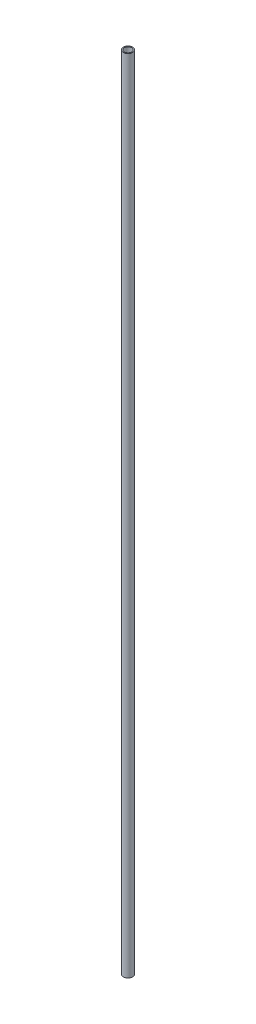
SolidWorks part; units mm, degrees
material "Thornel Mat VMA"
ref_plane "Front Plane" through (0, 0, 0) normal (0, 0, 1) x (1, 0, 0)
ref_plane "Top Plane" through (0, 0, 0) normal (0, 1, 0) x (1, 0, 0)
ref_plane "Right Plane" through (0, 0, 0) normal (1, 0, 0) x (0, 0, -1)
sketch "Sketch1" plane through (0, 0, 0) normal (0, 1, 0) x (1, 0, 0)
  circle A0 centre (0, 0) radius 3.6195
  circle A1 centre (0, 0) radius 2.8575
  dimension "D1" = 7.239
  dimension "D2" = 0.762
extrude "Boss-Extrude1" add sketch "Sketch1" along normal blind 622.3
